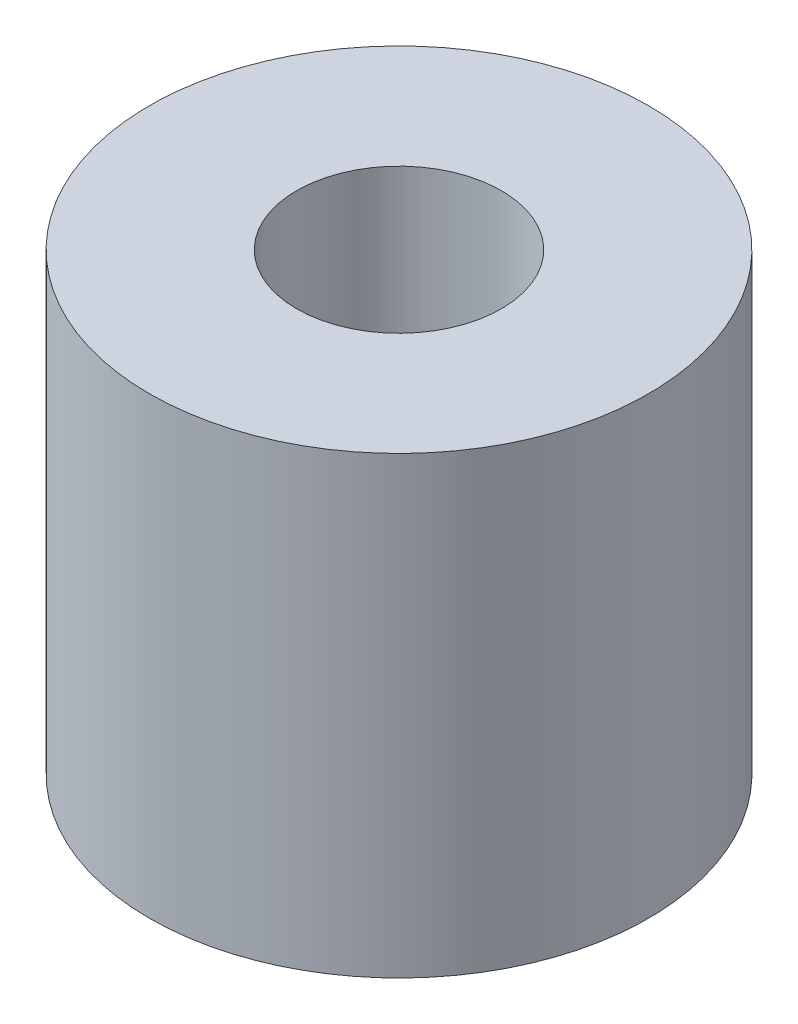
SolidWorks part; units mm, degrees
ref_plane "Front Plane" through (0, 0, 0) normal (0, 0, 1) x (1, 0, 0)
ref_plane "Top Plane" through (0, 0, 0) normal (0, 1, 0) x (1, 0, 0)
ref_plane "Right Plane" through (0, 0, 0) normal (1, 0, 0) x (0, 0, -1)
sketch "Sketch11" plane through (0, 0, 0) normal (0, 1, 0) x (1, 0, 0)
  circle A0 centre (0, 0) radius 1.6
  circle A1 centre (0, 0) radius 3.9
extrude "Boss-Extrude6" add sketch "Sketch11" along normal blind 7.1
